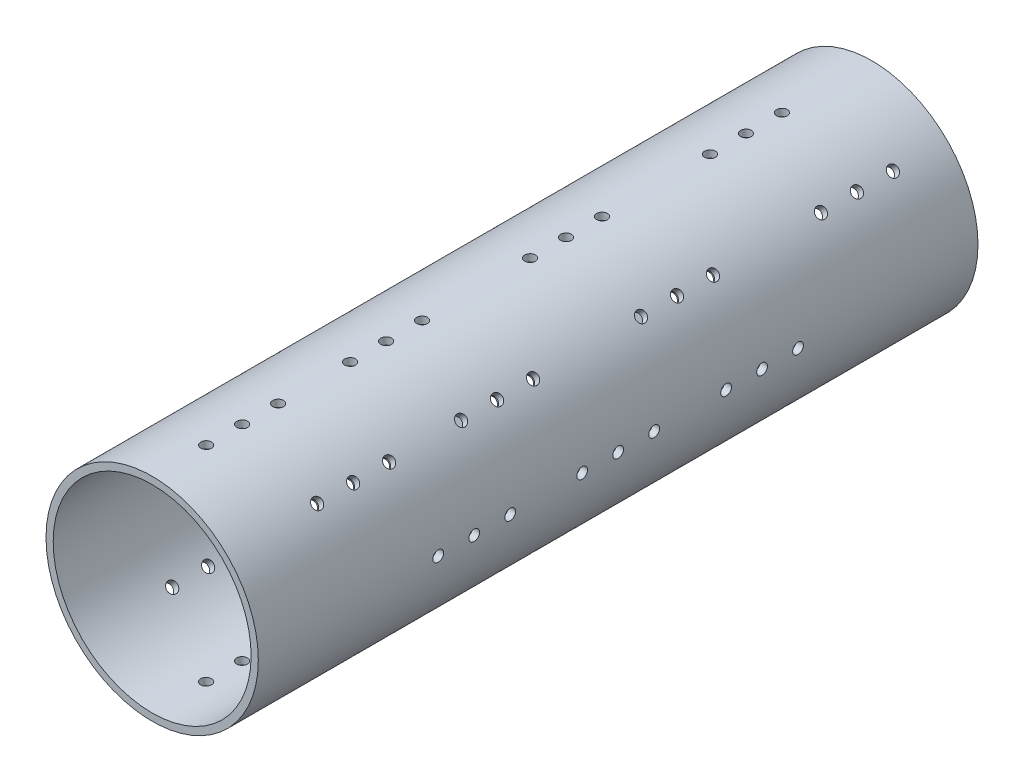
SolidWorks part; units mm, degrees
ref_plane "Front Plane" through (0, 0, 0) normal (0, 0, 1) x (1, 0, 0)
ref_plane "Top Plane" through (0, 0, 0) normal (0, 1, 0) x (1, 0, 0)
ref_plane "Right Plane" through (0, 0, 0) normal (1, 0, 0) x (0, 0, -1)
sketch "Sketch1" plane through (0, 0, 0) normal (0, 0, 1) x (1, 0, 0)
  circle A0 centre (0, 0) radius 27.5
  circle A1 centre (0, 0) radius 29.5
  dimension "D1" = 55
  dimension "D2" = 59
extrude "Boss-Extrude1" add sketch "Sketch1" along normal mid plane 200
sketch "Sketch2" plane through (0, 0, 0) normal (0, 1, 0) x (1, 0, 0)
  line L0 (0, -45) -> (0, -25) construction
  line L1 (-29.5, -100) -> (29.5, -100) construction
  circle A0 centre (0, -45) radius 1.5
  circle A1 centre (0, -35) radius 1.5
  circle A2 centre (0, -25) radius 1.5
  dimension "D1" = 3
  dimension "D2" = 10
  dimension "D3" = 10
  dimension "D4" = 55
extrude "Cut-Extrude1" cut sketch "Sketch2" against normal through all both and the other way through all
sketch "Sketch3" plane through (0, 0, 0) normal (1, 0, 0) x (0, 0, -1)
  line L0 (-100, 0) -> (100, 0) construction
  line L1 (-100, 29.5) -> (-100, -29.5) construction
  line L2 (0, 0) -> (50000, 0) construction
  circle A0 centre (-10, 0) radius 1.5
  circle A1 centre (0, 0) radius 1.5
  circle A2 centre (10, 0) radius 1.5
  dimension "D4" = 3
  dimension "D1" = 10
  dimension "D2" = 10
  dimension "D3" = 90
extrude "Cut-Extrude2" cut sketch "Sketch3" against normal through all both and the other way through all
ref_plane "Plane1" through (0, 0, 0) normal (0.7071, 0.7071, 0) x (0, 0, -1)
sketch "Sketch6" plane through (0, 0, 0) normal (0.7071, 0.7071, 0) x (0, 0, -1)
  line L0 (0, 0) -> (-50000, 0) construction
  line L2 (-100, 29.5) -> (-100, -29.5) construction
  circle A0 centre (-15, 0) radius 1.5
  circle A1 centre (-25, 0) radius 1.5
  circle A2 centre (-35, 0) radius 1.5
  dimension "D4" = 3
  dimension "D1" = 10
  dimension "D2" = 10
  dimension "D3" = 65
extrude "Cut-Extrude3" cut sketch "Sketch6" against normal through all both and the other way through all
ref_plane "Plane2" through (0, 0, 0) normal (0.7071, -0.7071, 0) x (0, 0, -1)
sketch "Sketch7" plane through (0, 0, 0) normal (0.7071, -0.7071, 0) x (0, 0, -1)
  line L0 (-100, 0) -> (100, 0) construction
  line L1 (100, -29.5) -> (100, 29.5) construction
  circle A0 centre (35, 0) radius 1.5
  circle A1 centre (25, 0) radius 1.5
  circle A2 centre (15, 0) radius 1.5
  dimension "D1" = 10
  dimension "D2" = 10
  dimension "D4" = 3
  dimension "D3" = 65
extrude "Cut-Extrude4" cut sketch "Sketch7" against normal through all both and the other way through all
pattern_linear "LPattern1" count 3 spacing 50 along (0, 0, -1) count 2 spacing 40 along (0, 0, 1) of "Cut-Extrude1", "Cut-Extrude3"
pattern_linear "LPattern2" count 3 spacing 40 along (0, 0, 1) count 2 spacing 40 along (0, 0, -1) of "Cut-Extrude4"
pattern_linear "LPattern3" count 2 spacing 40 along (0, 0, -1) count 2 spacing 40 along (0, 0, 1) of "Cut-Extrude2"
